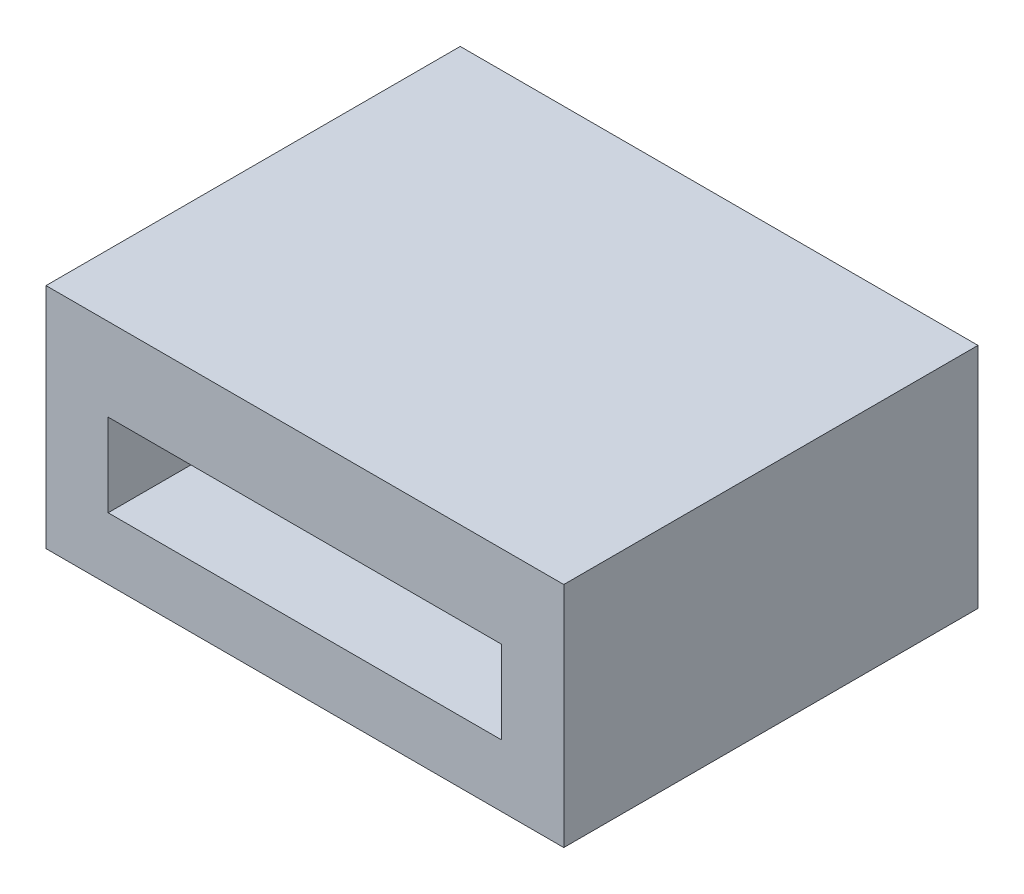
SolidWorks part; units mm, degrees
ref_plane "Front Plane" through (0, 0, 0) normal (0, 0, 1) x (1, 0, 0)
ref_plane "Top Plane" through (0, 0, 0) normal (0, 1, 0) x (1, 0, 0)
ref_plane "Right Plane" through (0, 0, 0) normal (1, 0, 0) x (0, 0, -1)
sketch "Sketch1" plane through (0, 0, 0) normal (0, 1, 0) x (1, 0, 0)
  line L1 (0, 0) -> (25, 0)
  line L2 (0, 0) -> (0, 20)
  line L3 (0, 20) -> (25, 20)
  line L4 (25, 0) -> (25, 20)
  line L5 (0, 0) -> (25, 20) construction
  line L6 (0, 20) -> (25, 0) construction
  point P4 (12.5, 10)
  dimension "D1" = 25
  dimension "D2" = 20
extrude "Boss-Extrude1" add sketch "Sketch1" along normal blind 3 contours L3 L4 L1 L2
sketch "Sketch2" plane through (0, 3, 0) normal (0, 1, 0) x (1, 0, 0)
  line L0 (0, 0) -> (25, 0) construction
  line L1 (0, 20) -> (3, 20)
  line L2 (0, 20) -> (0, 0)
  line L3 (0, 0) -> (3, 0)
  line L4 (3, 20) -> (3, 0)
  line L5 (0, 20) -> (3, 0) construction
  line L6 (0, 0) -> (3, 20) construction
  line L7 (0, 20) -> (25, 20) construction
  line L8 (22, 20) -> (25, 20)
  line L9 (22, 20) -> (22, 0)
  line L10 (22, 0) -> (25, 0)
  line L11 (25, 20) -> (25, 0)
  line L12 (22, 20) -> (25, 0) construction
  line L13 (22, 0) -> (25, 20) construction
  point P4 (1.5, 10)
  point P12 (23.5, 10)
  dimension "D1" = 3
extrude "Boss-Extrude2" add sketch "Sketch2" along normal blind 4
sketch "Sketch3" plane through (0, 7, 0) normal (0, 1, 0) x (1, 0, 0)
  line L1 (0, 20) -> (25, 20)
  line L2 (0, 20) -> (0, 0)
  line L3 (0, 0) -> (25, 0)
  line L4 (25, 20) -> (25, 0)
  line L5 (0, 20) -> (25, 0) construction
  line L6 (0, 0) -> (25, 20) construction
  point P4 (12.5, 10)
extrude "Boss-Extrude3" add sketch "Sketch3" along normal blind 4
